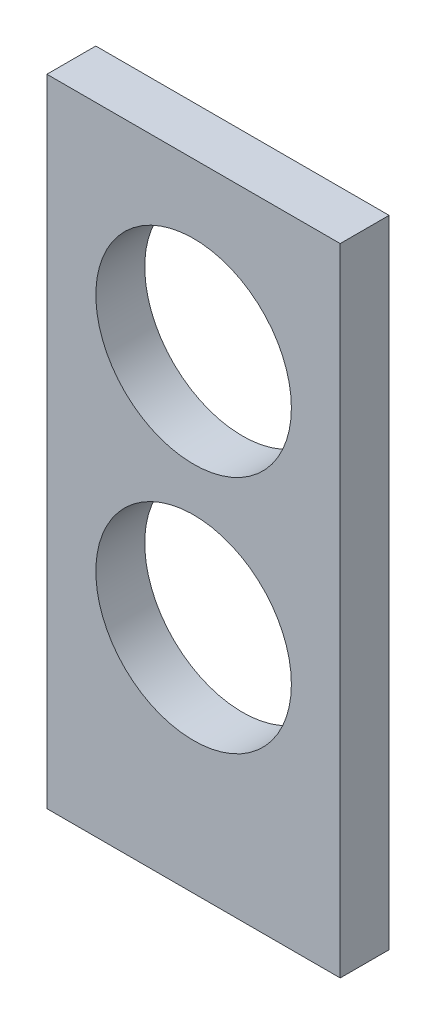
SolidWorks part; units mm, degrees
ref_plane "Front Plane" through (0, 0, 0) normal (0, 0, 1) x (1, 0, 0)
ref_plane "Top Plane" through (0, 0, 0) normal (0, 1, 0) x (1, 0, 0)
ref_plane "Right Plane" through (0, 0, 0) normal (1, 0, 0) x (0, 0, -1)
sketch "Sketch1" plane through (0, 0, 0) normal (0, 0, 1) x (1, 0, 0)
  line L0 (-15.0055, -40.5861) -> (-15.0055, 24.4702)
  line L1 (-15.0055, -40.5861) -> (14.9945, -40.5861)
  line L7 (-15.0055, 24.4702) -> (14.9945, 24.4702)
  line L8 (14.9945, 24.4702) -> (14.9945, -40.5861)
  circle A0 centre (0, 7.4228) radius 10
  circle A1 centre (0, -17.0545) radius 10
  point P0 (0, 0)
extrude "Boss-Extrude1" add sketch "Sketch1" along normal blind 5
